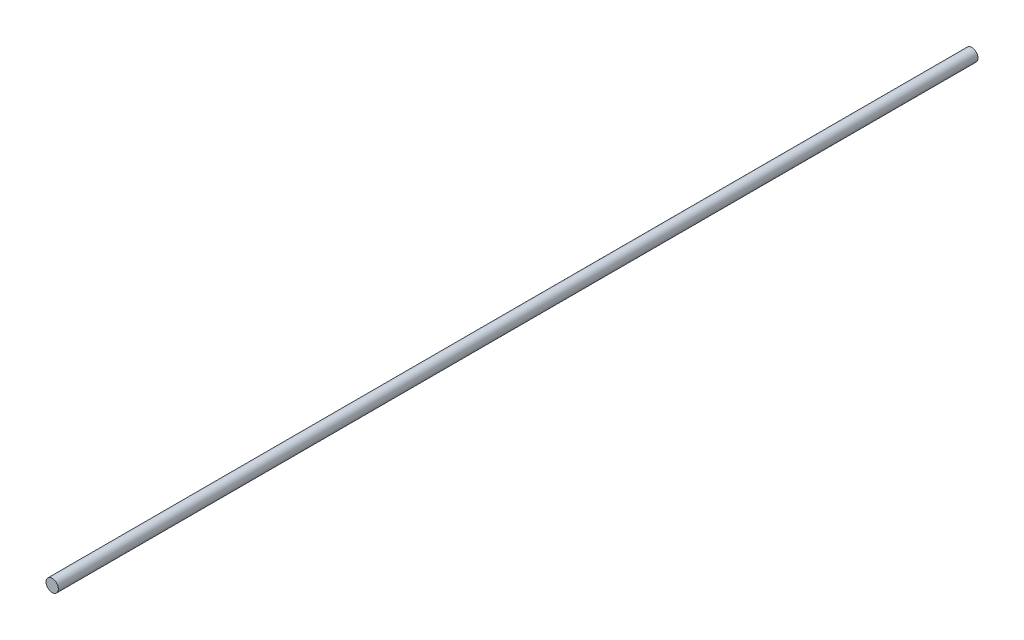
SolidWorks part; units mm, degrees
ref_plane "Front Plane" through (0, 0, 0) normal (0, 0, 1) x (1, 0, 0)
ref_plane "Top Plane" through (0, 0, 0) normal (0, 1, 0) x (1, 0, 0)
ref_plane "Right Plane" through (0, 0, 0) normal (1, 0, 0) x (0, 0, -1)
sketch "Sketch1" plane through (0, 0, 0) normal (0, 0, 1) x (1, 0, 0)
  circle A0 centre (0, 0) radius 3.175
  dimension "D1" = 6.35
extrude "Boss-Extrude1" add sketch "Sketch1" along normal blind 472.435
